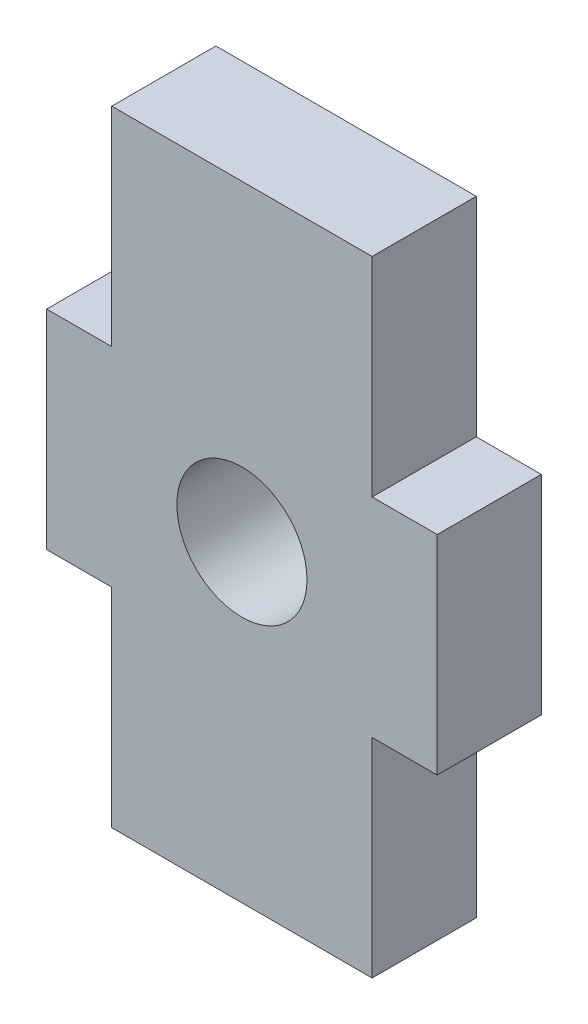
SolidWorks part; units mm, degrees
ref_plane "Front Plane" through (0, 0, 0) normal (0, 0, 1) x (1, 0, 0)
ref_plane "Top Plane" through (0, 0, 0) normal (0, 1, 0) x (1, 0, 0)
ref_plane "Right Plane" through (0, 0, 0) normal (1, 0, 0) x (0, 0, -1)
sketch "Sketch1" plane through (0, 0, 0) normal (0, 0, 1) x (1, 0, 0)
  line L0 (1952.1768, 1466.8841) -> (1957.1768, 1466.8841)
  line L1 (1952.1768, 1454.8841) -> (1957.1768, 1454.8841)
  line L3 (1957.1768, 1458.8841) -> (1957.1768, 1454.8841)
  line L4 (1957.1768, 1458.8841) -> (1958.4268, 1458.8841)
  line L5 (1958.4268, 1462.8841) -> (1958.4268, 1458.8841)
  line L6 (1957.1768, 1462.8841) -> (1957.1768, 1466.8841)
  line L7 (1957.1768, 1462.8841) -> (1958.4268, 1462.8841)
  line L37 (1952.1768, 1458.8841) -> (1950.9268, 1458.8841)
  line L40 (1952.1768, 1458.8841) -> (1952.1768, 1454.8841)
  line L127 (1952.1768, 1462.8841) -> (1950.9268, 1462.8841)
  line L130 (1952.1768, 1462.8841) -> (1952.1768, 1466.8841)
  line L131 (1950.9268, 1462.8841) -> (1950.9268, 1458.8841)
  circle A82 centre (1954.6768, 1460.8841) radius 1.25
  dimension "D1" = 2.5
  dimension "D2" = 1950.9268
  dimension "D3" = 1954.6768
  dimension "D4" = 1957.1768
  dimension "D5" = 1454.8841
  dimension "D6" = 1458.8841
  dimension "D7" = 1460.8841
extrude "Boss-Extrude1" add sketch "Sketch1" along normal blind 2
